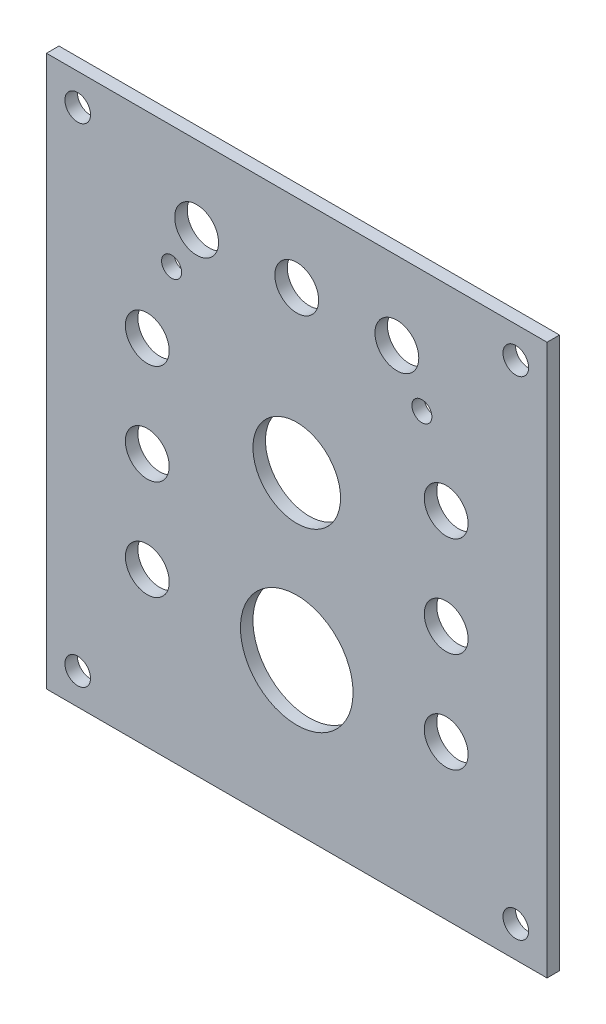
SolidWorks part; units mm, degrees
ref_plane "Front Plane" through (0, 0, 0) normal (0, 0, 1) x (1, 0, 0)
ref_plane "Top Plane" through (0, 0, 0) normal (0, 1, 0) x (1, 0, 0)
ref_plane "Right Plane" through (0, 0, 0) normal (1, 0, 0) x (0, 0, -1)
ref_plane "Plane1" through (0, 0, -3.175) normal (0, 0, -1) x (-1, 0, 0)
sketch "Sketch1" plane through (0, 0, -3.175) normal (0, 0, -1) x (-1, 0, 0)
  line L0 (-63.5, -38.1) -> (63.5, -38.1)
  line L1 (63.5, -38.1) -> (63.5, 101.6)
  line L2 (63.5, 101.6) -> (-63.5, 101.6)
  line L3 (-63.5, 101.6) -> (-63.5, -38.1)
  circle A0 centre (55.5752, -30.1752) radius 3.2512
  circle A1 centre (0, 81.8388) radius 5.5626
  circle A2 centre (37.9152, 51.7772) radius 5.5626
  circle A3 centre (-37.9152, 0.9772) radius 5.5626
  circle A4 centre (-25.4, 81.8388) radius 5.5626
  circle A5 centre (0, 41.148) radius 11.1125
  circle A6 centre (-55.5752, 93.6752) radius 3.2512
  circle A7 centre (-55.5752, -30.1752) radius 3.2512
  circle A8 centre (55.5752, 93.6752) radius 3.2512
  circle A9 centre (0, 0) radius 14.2875
  circle A10 centre (25.4, 81.8388) radius 5.5626
  circle A11 centre (-37.9152, 51.7772) radius 5.5626
  circle A12 centre (37.9152, 0.9772) radius 5.5626
  circle A13 centre (37.9152, 26.3772) radius 5.5626
  circle A14 centre (-37.9152, 26.3772) radius 5.5626
  circle A15 centre (31.75, 70.5802) radius 2.54
  circle A16 centre (-31.75, 70.5802) radius 2.54
extrude "Boss-Extrude1" add sketch "Sketch1" against normal blind 3.175
sketch "Sketch3" plane through (0, 0, 0) normal (0, 0, 1) x (1, 0, 0)
  line L0 (0, -38.1) -> (0, -14.2875) construction
  line L1 (63.5, -38.1) -> (-63.5, -38.1) construction
  circle A0 centre (0, 0) radius 14.2875 construction
  point P7 (0, 0)
